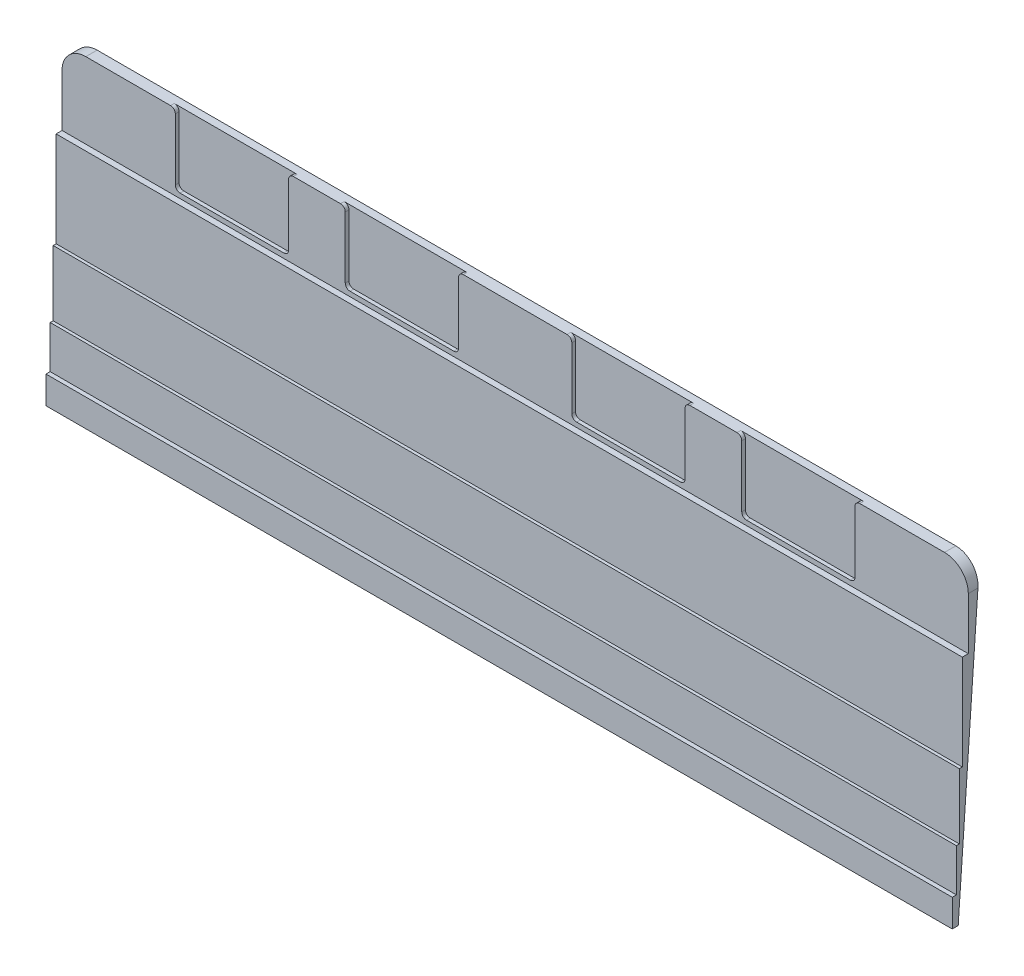
SolidWorks part; units mm, degrees
material "Glass"
ref_plane "Front Plane" through (0, 0, 0) normal (0, 0, 1) x (1, 0, 0)
ref_plane "Top Plane" through (0, 0, 0) normal (0, 1, 0) x (1, 0, 0)
ref_plane "Right Plane" through (0, 0, 0) normal (1, 0, 0) x (0, 0, -1)
ref_plane "Plane1" through (-149.225, 0, 0) normal (-1, 0, 0) x (0, 0, 1)
ref_plane "Plane2" through (155.5753, 0, 0) normal (1, 0, 0) x (0, 0, -1)
sketch "Sketch1" plane through (-149.225, 0, 0) normal (-1, 0, 0) x (0, 0, 1)
  line L1 (-2, -64.3742) -> (-3.3962, -64.3742)
  line L2 (-4, 84.0184) -> (-4, -73.6248) construction
  line L3 (-4, -73.6248) -> (-11.2027, 29.3782)
  line L4 (-3.3962, -64.3742) -> (-3.3962, -50.0488)
  line L5 (14.1038, -73.6248) -> (-62.5482, -73.6248) construction
  line L6 (-4, -73.6248) -> (-15.0962, 85.0583) construction
  line L7 (-3.3962, -50.0488) -> (-4.3962, -50.0488)
  line L9 (-4.3962, -50.0488) -> (-4.3962, -28.1263)
  line L10 (-4.3962, -28.1263) -> (-5.3962, -28.1263)
  line L11 (-0.1, -64.3742) -> (-4.1456, -64.3742) construction
  line L14 (-2, -73.6248) -> (-4, -73.6248)
  line L16 (-2, -73.6248) -> (-2, -64.3742)
  line L17 (-5.3962, -28.1263) -> (-5.3962, 3.8737)
  line L19 (-5.3962, 3.8737) -> (-7.3962, 3.8737)
  line L20 (-7.3962, 3.8737) -> (-7.3962, 29.3782)
  line L21 (-7.3962, 29.3782) -> (-11.2027, 29.3782)
  point P18 (0, 0)
  dimension "D1" = 73.6248
  dimension "D2" = 2
  dimension "D3" = 4
extrude "Boss-Extrude1" add sketch "Sketch1" against normal up to surface (304.8003 mm away) up to plane "Plane2"
fillet "Fillet1" radius 8 2 edges at (155.5753, 29.3782, -9.2994) (-149.225, 29.3782, -9.2994)
sketch "Sketch2" plane through (0, 0, -7.3962) normal (0, 0, 1) x (1, 0, 0)
  line L0 (3.1753, 121.2498) -> (3.1753, -113.2057) construction
  line L1 (10.1748, 54.6246) -> (-3.8242, 54.6246) construction
  line L2 (60.3261, 5.4737) -> (22.2253, 5.4737)
  line L3 (-104.1252, 35.5747) -> (-118.1245, 35.5747) construction
  line L12 (-111.1249, 5.4737) -> (-111.1249, 29.3782)
  line L13 (-111.1249, 29.3782) -> (-73.0249, 29.3782)
  line L14 (-73.0249, 29.3782) -> (-73.0249, 5.4737)
  line L15 (-66.0252, 35.5747) -> (-80.0245, 35.5747) construction
  line L16 (-53.9756, 5.4737) -> (-53.9756, 29.3782)
  line L17 (-53.9756, 29.3782) -> (-15.8747, 29.3782)
  line L18 (-15.8747, 29.3782) -> (-15.8747, 5.4737)
  line L19 (-46.9752, 35.5747) -> (-60.9759, 35.5747) construction
  line L20 (-8.8752, 35.5747) -> (-22.8742, 35.5747) construction
  line L21 (-111.1249, 5.4737) -> (-73.0249, 5.4737)
  line L22 (-53.9756, 5.4737) -> (-15.8747, 5.4737)
  line L23 (117.4754, 5.4737) -> (79.3754, 5.4737)
  line L24 (22.2253, 29.3782) -> (22.2253, 5.4737)
  line L25 (60.3261, 29.3782) -> (22.2253, 29.3782)
  line L26 (60.3261, 5.4737) -> (60.3261, 29.3782)
  line L27 (79.3754, 29.3782) -> (79.3754, 5.4737)
  line L28 (117.4754, 29.3782) -> (79.3754, 29.3782)
  line L29 (117.4754, 5.4737) -> (117.4754, 29.3782)
  line L31 (147.5753, 29.3782) -> (-141.225, 29.3782) construction
  line L33 (155.5753, 3.8737) -> (-149.225, 3.8737) construction
  point P12 (3.1753, 54.6246)
  point P24 (-111.1249, 35.5747)
  point P27 (-73.0249, 35.5747)
  point P30 (-53.9756, 35.5747)
  point P33 (-15.8747, 35.5747)
  dimension "D1" = 1.6
extrude "Cut-Extrude1" cut sketch "Sketch2" against normal blind 1.25
fillet "Fillet2" radius 1.6 8 edges at (-15.8747, 5.4737, -8.0212) (-53.9756, 5.4737, -8.0212) (-111.1249, 5.4737, -8.0212) (-73.0249, 5.4737, -8.0212) (79.3754, 5.4737, -8.0212) (117.4754, 5.4737, -8.0212) (60.3261, 5.4737, -8.0212) (22.2253, 5.4737, -8.0212)
fillet "Fillet3" radius 1.6 8 edges at (117.4754, 29.3782, -8.0212) (60.3261, 29.3782, -8.0212) (79.3754, 29.3782, -8.0212) (22.2253, 29.3782, -8.0212) (-15.8747, 29.3782, -8.0212) (-53.9756, 29.3782, -8.0212) (-73.0249, 29.3782, -8.0212) (-111.1249, 29.3782, -8.0212)
